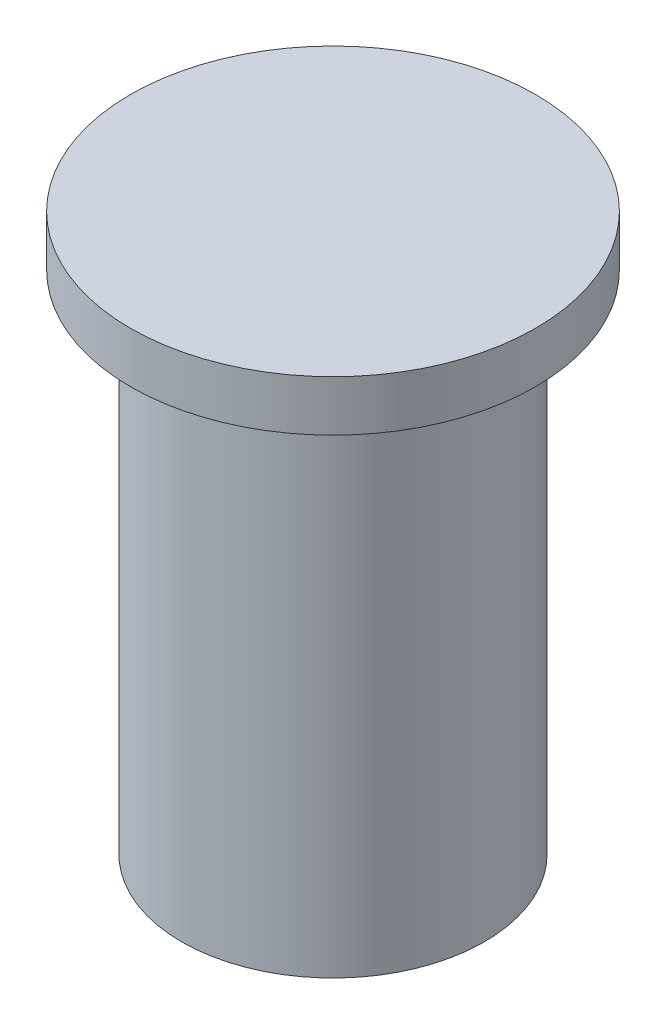
SolidWorks part; units mm, degrees
ref_plane "Front Plane" through (0, 0, 0) normal (0, 0, 1) x (1, 0, 0)
ref_plane "Top Plane" through (0, 0, 0) normal (0, 1, 0) x (1, 0, 0)
ref_plane "Right Plane" through (0, 0, 0) normal (1, 0, 0) x (0, 0, -1)
sketch "Sketch1" plane through (0, 0, 0) normal (0, 1, 0) x (1, 0, 0)
  circle A0 centre (0, 0) radius 44.85
  dimension "D1" = 89.7
extrude "Boss-Extrude1" add sketch "Sketch1" along normal blind 150
sketch "Sketch4" plane through (0, 150, 0) normal (0, 1, 0) x (1, 0, 0)
  circle A0 centre (0, 0) radius 60
  dimension "D1" = 120
extrude "Boss-Extrude3" add sketch "Sketch4" along normal blind 15
